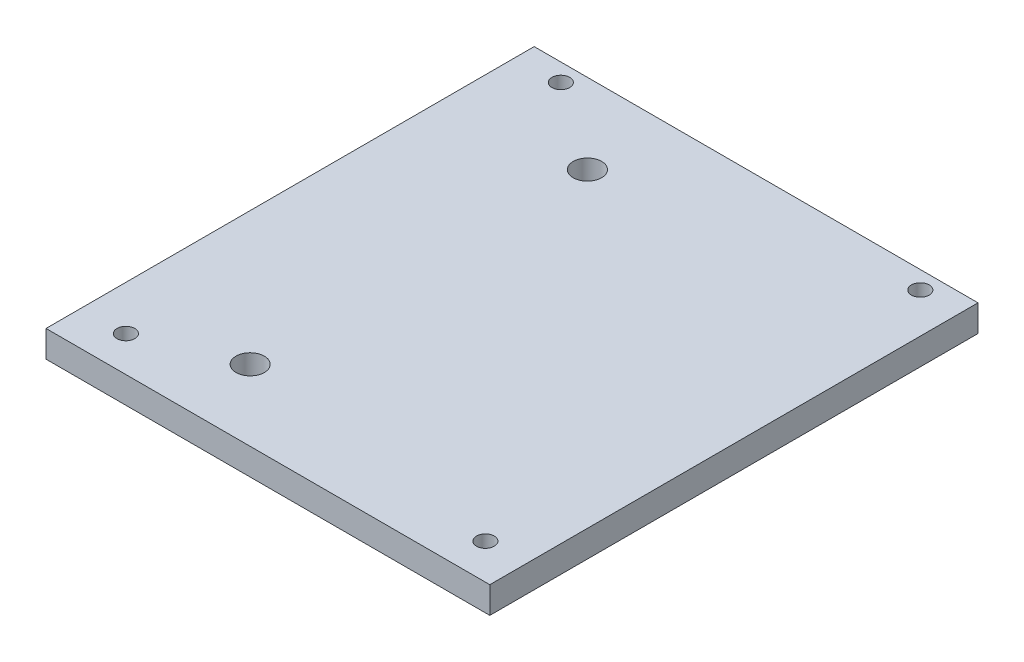
SolidWorks part; units mm, degrees
ref_plane "Front Plane" through (0, 0, 0) normal (0, 0, 1) x (1, 0, 0)
ref_plane "Top Plane" through (0, 0, 0) normal (0, 1, 0) x (1, 0, 0)
ref_plane "Right Plane" through (0, 0, 0) normal (1, 0, 0) x (0, 0, -1)
sketch "Sketch1" plane through (0, 0, 0) normal (0, 1, 0) x (1, 0, 0)
  line L0 (-29.511, 20.1848) -> (-29.511, -17.8152) construction
  line L1 (-44.511, 29.1848) -> (5.489, 29.1848)
  line L2 (-44.511, 29.1848) -> (-44.511, -25.8152)
  line L3 (-44.511, -25.8152) -> (5.489, -25.8152)
  line L4 (5.489, 29.1848) -> (5.489, -25.8152)
  line L6 (-39.511, 27.1848) -> (0.989, 27.1848) construction
  line L7 (-39.511, 27.1848) -> (-39.511, -21.8152) construction
  line L8 (-39.511, -21.8152) -> (0.989, -21.8152) construction
  line L9 (0.989, 27.1848) -> (0.989, -21.8152) construction
  circle A0 centre (-29.511, 20.1848) radius 1.6
  circle A1 centre (-29.511, -17.8152) radius 1.6
  circle A2 centre (-39.511, 27.1848) radius 1
  circle A3 centre (-39.511, -21.8152) radius 1
  circle A4 centre (0.989, -21.8152) radius 1
  circle A5 centre (0.989, 27.1848) radius 1
  dimension "D3" = 3.2
  dimension "D4" = 3.2
  dimension "D12" = 2
  dimension "D1" = 9
  dimension "D2" = 50
  dimension "D5" = 38
  dimension "D6" = 8
  dimension "D7" = 15
  dimension "D8" = 4
  dimension "D9" = 10
  dimension "D10" = 40.5
  dimension "D11" = 49
extrude "Boss-Extrude1" add sketch "Sketch1" along normal blind 3
